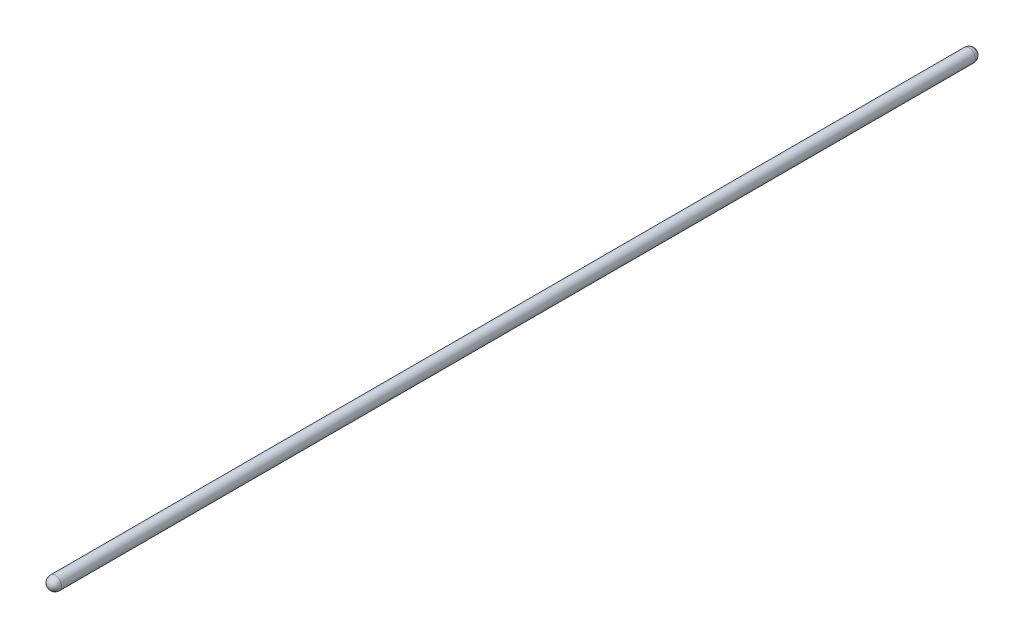
SolidWorks part; units mm, degrees
ref_plane "Front Plane" through (0, 0, 0) normal (0, 0, 1) x (1, 0, 0)
ref_plane "Top Plane" through (0, 0, 0) normal (0, 1, 0) x (1, 0, 0)
ref_plane "Right Plane" through (0, 0, 0) normal (1, 0, 0) x (0, 0, -1)
sketch "Sketch1" plane through (0, 0, 0) normal (0, 1, 0) x (1, 0, 0)
  line L0 (0, 0) -> (0, 9.525) construction
  line L1 (0, 0) -> (9.525, 0) construction
  line L2 (0, 0) -> (0, -1346.344) construction
  line L3 (0, -1346.344) -> (9.525, -1346.344) construction
  line L4 (0, -1346.344) -> (0, -1355.869) construction
  line L5 (9.525, 0) -> (9.525, -1346.344)
  line L6 (0, 9.525) -> (0, -1355.869)
  arc A1 (0, 9.525) -> (9.525, 0) centre (0, 0) cw
  arc A2 (9.525, -1346.344) -> (0, -1355.869) centre (0, -1346.344) cw
revolve "Revolve1" add sketch "Sketch1" angle 360 about L6
